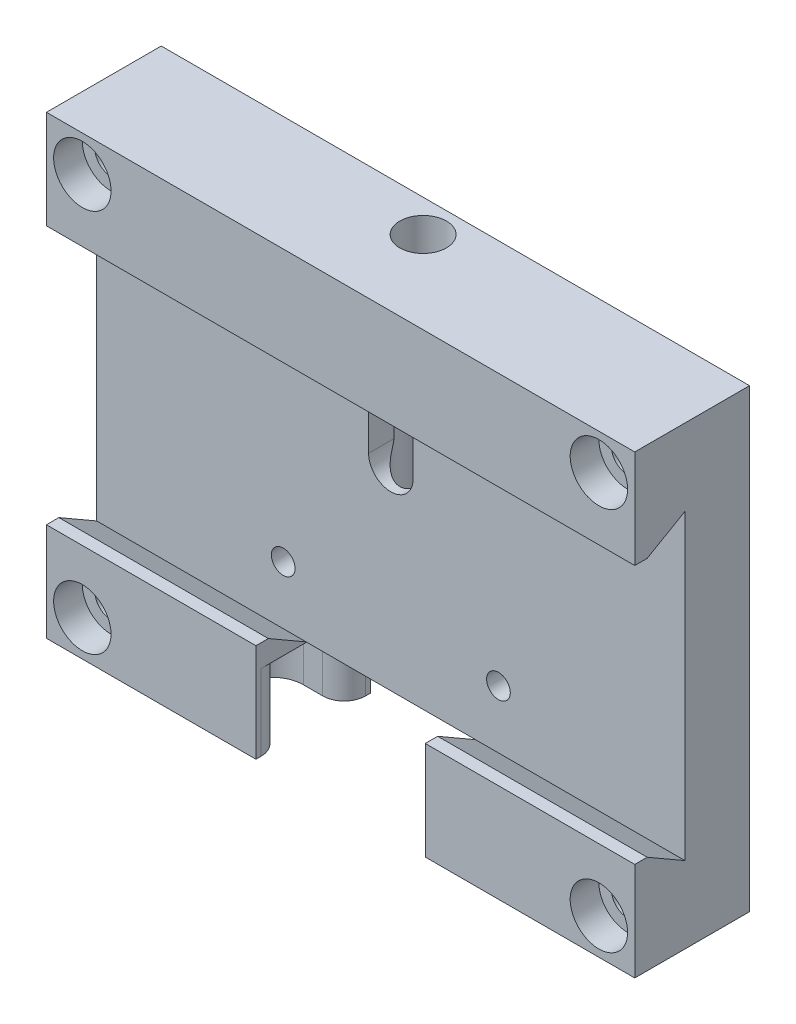
SolidWorks part; units mm, degrees
material "Сплав 2024"
ref_plane "Спереди" through (0, 0, 0) normal (0, 0, 1) x (1, 0, 0)
ref_plane "Сверху" through (0, 0, 0) normal (0, 1, 0) x (1, 0, 0)
ref_plane "Справа" through (0, 0, 0) normal (1, 0, 0) x (0, 0, -1)
sketch "Эскиз1" plane through (0, 0, 0) normal (0, 0, 1) x (1, 0, 0)
  line L1 (0, 0) -> (82, 0)
  line L2 (0, 0) -> (0, -63.5)
  line L3 (0, -63.5) -> (82, -63.5)
  line L4 (82, 0) -> (82, -63.5)
  dimension "D1" = 63.5
  dimension "D2" = 82
extrude "Бобышка-Вытянуть1" add sketch "Эскиз1" along normal blind 16
sketch "Эскиз2" plane through (0, 0, 0) normal (-1, 0, 0) x (0, 0, 1)
  line L0 (0, -31.75) -> (12.8711, -31.75) construction
  line L1 (0, 0) -> (0, -63.5) construction
  line L3 (16, 0) -> (16, -63.5) construction
  line L4 (9, -10.67) -> (16, -14.7115)
  line L5 (9, -10.67) -> (9, -52.83)
  line L6 (9, -52.83) -> (16, -48.7885)
  line L7 (16, -14.7115) -> (16, -48.7885)
  line L8 (9, -10.67) -> (16, -48.7885) construction
  line L9 (9, -52.83) -> (16, -14.7115) construction
  dimension "D1" = 42.16
  dimension "D2" = 60
  dimension "D3" = 60
  dimension "D4" = 7
extrude "Вырез-Вытянуть1" cut sketch "Эскиз2" against normal through all
ref_plane "Плоскость1" through (0, 0, 4) normal (0, 0, 1) x (1, 0, 0)
sketch "Эскиз11" plane through (0, 0, 0) normal (0, 0, -1) x (-1, 0, 0)
  line L0 (-82, -5) -> (0, -5) construction
  line L1 (-82, -63.5) -> (-82, 0) construction
  line L2 (0, 0) -> (0, -63.5) construction
  line L3 (-82, -58.5) -> (0, -58.5) construction
  line L4 (-82, 0) -> (0, 0) construction
  line L5 (0, -63.5) -> (-82, -63.5) construction
  line L8 (-82, -31.75) -> (0, -31.75) construction
  line L9 (-41, 0) -> (-41, -63.5) construction
  line L10 (-77, 0) -> (-77, -63.5) construction
  line L11 (-63.5, -11.75) -> (-18.5, -11.75) construction
  line L12 (-63.5, -11.75) -> (-63.5, -51.75) construction
  line L13 (-63.5, -51.75) -> (-18.5, -51.75) construction
  line L14 (-18.5, -11.75) -> (-18.5, -51.75) construction
  line L15 (-63.5, -11.75) -> (-18.5, -51.75) construction
  line L16 (-63.5, -51.75) -> (-18.5, -11.75) construction
  line L17 (-82, 0) -> (0, 0) construction
  line L18 (-82, -10.67) -> (-82, -52.83) construction
  line L19 (-5, 0) -> (-5, -63.5) construction
  line L20 (0, -10.67) -> (0, -52.83) construction
  line L21 (0, -63.5) -> (-82, -63.5) construction
  point P20 (-41, -31.75)
  dimension "D1" = 5
  dimension "D2" = 5
  dimension "D3" = 5
  dimension "D4" = 5
  dimension "D5" = 45
  dimension "D6" = 40
sketch "Эскиз15" plane through (0, 0, 16) normal (0, 0, 1) x (1, 0, 0)
  line L0 (41, 0) -> (41, -63.5) construction
  line L1 (82, 0) -> (0, 0) construction
  line L2 (0, -63.5) -> (82, -63.5) construction
  line L3 (82, -48.7885) -> (0, -48.7885) construction
  line L4 (29.2, -48.7885) -> (52.8, -48.7885)
  line L5 (29.2, -48.7885) -> (29.2, -63.5)
  line L6 (29.2, -63.5) -> (52.8, -63.5)
  line L7 (52.8, -48.7885) -> (52.8, -63.5)
  line L8 (29.2, -48.7885) -> (52.8, -63.5) construction
  line L9 (29.2, -63.5) -> (52.8, -48.7885) construction
  point P6 (41, -56.1443)
  dimension "D1" = 23.6
extrude "Вырез-Вытянуть4" cut sketch "Эскиз15" against normal up to surface (7 mm away) up to face at (41, -31.75, 9)
sketch "Эскиз16" plane through (0, 0, 9) normal (0, 0, 1) x (1, 0, 0)
  line L0 (41, 0) -> (41, -63.5) construction
  line L1 (29.2, -52.83) -> (52.8, -52.83)
  line L2 (29.2, -52.83) -> (29.2, -63.5)
  line L3 (29.2, -63.5) -> (52.8, -63.5)
  line L4 (52.8, -52.83) -> (52.8, -63.5)
  line L5 (29.2, -52.83) -> (52.8, -63.5) construction
  line L6 (29.2, -63.5) -> (52.8, -52.83) construction
  line L7 (29.2, -63.5) -> (52.8, -63.5) construction
  line L8 (82, -52.83) -> (52.8, -52.83) construction
  line L9 (52.8, -63.5) -> (52.8, -52.83) construction
  point P0 (41, -58.165)
extrude "Вырез-Вытянуть5" cut sketch "Эскиз16" against normal up to surface (9 mm away) up to face at (41, -31.75, 0)
sketch "Эскиз17" plane through (0, -52.83, 0) normal (0, -1, 0) x (1, 0, 0)
  line L0 (35.125, 5) -> (60.125, 5) construction
  line L3 (41, 9) -> (41, 0) construction
  line L4 (82, 9) -> (0, 9) construction
  line L5 (29.2, 0) -> (52.8, 0) construction
  circle A0 centre (33.5, 5) radius 2.5
  circle A1 centre (48.5, 5) radius 2.5
  dimension "D1" = 5
  dimension "D2" = 7.5
  dimension "D3" = 5
extrude "Вырез-Вытянуть6" cut sketch "Эскиз17" against normal blind 8
hole_wizard "Отверстие обработанное метчиком M4x0.72" positions "Эскиз19" profile "Эскиз18" tap size "M4x0.7" standard "Ansi Metric"
sketch "Эскиз19" plane through (0, -52.83, 0) normal (0, -1, 0) x (-1, 0, 0)
  line L0 (-41, -9) -> (-41, 0) construction
  line L1 (-35.125, -5) -> (-60.125, -5) construction
  point P0 (-41, -5)
sketch "Эскиз18" plane through (41, -52.83, 5) normal (1, 0, 0) x (0, 0, -1)
  line L0 (0, 0) -> (0, 10.9914)
  line L1 (0, 10.9914) -> (1.65, 10)
  line L2 (1.65, 10) -> (1.65, 0)
  line L5 (1.65, 0) -> (0, 0)
  line L10 (0, 10.9914) -> (-1.65, 10) construction
  line L11 (0, -6.35) -> (0, 107.95) construction
  dimension "Диаметр сверла" = 3.3
  dimension "Глубина сверла" = 10
  dimension "Угол заточки сверла" = 118
cosmetic thread "Отверстие резьбы9" parameters "D1"=8, "D2"=4
sketch "Эскиз25" plane through (0, 0, 9) normal (0, 0, 1) x (1, 0, 0)
  line L0 (41, 0) -> (41, -52.83) construction
  line L1 (82, 0) -> (0, 0) construction
  line L2 (52.8, -52.83) -> (29.2, -52.83) construction
  line L3 (41, -18.7115) -> (41, -25.7115) construction
  line L4 (44.1, -18.7115) -> (44.1, -25.7115)
  line L5 (37.9, -18.7115) -> (37.9, -25.7115)
  line L6 (82, -14.7115) -> (0, -14.7115) construction
  arc A0 (44.1, -18.7115) -> (37.9, -18.7115) centre (41, -18.7115) ccw
  arc A1 (37.9, -25.7115) -> (44.1, -25.7115) centre (41, -25.7115) ccw
  point P8 (41, -22.2115)
  dimension "D1" = 3.1
  dimension "D2" = 4
  dimension "D3" = 7
extrude "Вырез-Вытянуть7" cut sketch "Эскиз25" against normal blind 4
sketch "Эскиз26" plane through (0, 0, 0) normal (0, 1, 0) x (1, 0, 0)
  line L0 (0, -9) -> (82, -9) construction
  line L1 (0, -16) -> (0, 0) construction
  line L2 (82, -16) -> (82, 0) construction
  line L4 (82, 0) -> (0, 0) construction
  line L5 (41, 0) -> (41, -16) construction
  line L6 (82, -16) -> (0, -16) construction
  circle A0 centre (41, -4.5) radius 3.25
  dimension "D2" = 6.5
  dimension "D1" = 9
  dimension "D3" = 4.5
extrude "Вырез-Вытянуть8" cut sketch "Эскиз26" against normal blind 38
hole_wizard "Цековка для винта с внутренним шестигранником M41" positions "Эскиз29" profile "Эскиз28" counterbore size "M4" standard "Ansi Metric" end condition through all
sketch "Эскиз29" plane through (30.7592, 26.7934, 16) normal (0, 0, -1) x (-1, 0, 0)
  line L0 (-51.2408, -31.7934) -> (30.7592, -31.7934) construction
  line L1 (-46.2408, -26.7934) -> (-46.2408, -90.2934) construction
  line L2 (-51.2408, -85.2934) -> (30.7592, -85.2934) construction
  line L3 (25.7592, -26.7934) -> (25.7592, -90.2934) construction
  point P0 (-46.2408, -31.7934)
  point P6 (-46.2408, -85.2934)
  point P10 (25.7592, -85.2934)
  point P14 (25.7592, -31.7934)
sketch "Эскиз28" plane through (77, -5, 16) normal (1, 0, 0) x (0, -1, 0)
  line L0 (0, 0) -> (0, 16)
  line L1 (0, 16) -> (2.25, 16)
  line L3 (2.25, 16) -> (2.25, 4)
  line L4 (2.25, 4) -> (4, 4)
  line L5 (4, 4) -> (4, 0)
  line L7 (4, 0) -> (0, 0)
  line L11 (0, -6.35) -> (0, 107.95) construction
  dimension "Диаметр сквозного отверстия" = 4.5
  dimension "Глубина сквозного отверстия" = 16
  dimension "Диаметр цековки" = 8
  dimension "Глубина цековки" = 4
chamfer "Фаска2" distance 1 angle 90 3 edges at (67.4, -48.7885, 16) (14.6, -48.7885, 16) (41, -14.7115, 16)
sketch "Эскиз32" plane through (0, -63.5, 0) normal (0, -1, 0) x (1, 0, 0)
  line L0 (52.7, -0.2) -> (52.7, 3.7)
  line L1 (41, 9) -> (41, 0) construction
  line L2 (52.8, 9) -> (29.2, 9) construction
  line L3 (52.5, 0) -> (52.5, 3.9) construction
  line L4 (29.2, 8) -> (52.8, 8) construction
  line L5 (52.5, 3.9) -> (58.5, 3.9) construction
  line L6 (58.5, 12.1) -> (52.5, 12.1) construction
  line L7 (29.2, 0) -> (29.2, 16) construction
  line L8 (52.8, 0) -> (52.8, 9) construction
  line L9 (52.5, 12.1) -> (52.5, 16) construction
  line L10 (52.5, 16) -> (29.5, 16) construction
  line L11 (29.5, 16) -> (29.5, 12.1) construction
  line L12 (29.5, 12.1) -> (23.5, 12.1) construction
  line L13 (23.5, 3.9) -> (29.5, 3.9) construction
  line L14 (29.5, 3.9) -> (29.5, 0) construction
  line L15 (29.5, 0) -> (52.5, 0) construction
  line L16 (52.7, 3.7) -> (58.5, 3.7)
  line L17 (58.5, 12.3) -> (52.7, 12.3)
  line L18 (52.7, 12.3) -> (52.7, 16.2)
  line L19 (52.7, 16.2) -> (29.3, 16.2)
  line L20 (29.3, 16.2) -> (29.3, 12.3)
  line L21 (29.3, 12.3) -> (23.5, 12.3)
  line L22 (23.5, 3.7) -> (29.3, 3.7)
  line L23 (29.3, 3.7) -> (29.3, -0.2)
  line L24 (29.3, -0.2) -> (52.7, -0.2)
  arc A0 (58.5, 3.9) -> (58.5, 12.1) centre (58.5, 8) ccw construction
  arc A1 (23.5, 12.1) -> (23.5, 3.9) centre (23.5, 8) ccw construction
  arc A2 (58.5, 3.7) -> (58.5, 12.3) centre (58.5, 8) ccw
  arc A3 (23.5, 12.3) -> (23.5, 3.7) centre (23.5, 8) ccw
  point P7 (41, 16)
  point P20 (41, 0)
  dimension "D1" = 0.2
extrude "Вырез-Вытянуть12" cut sketch "Эскиз32" against normal blind 10.6
fillet "Скругление1" radius 3 4 edges at (52.8, -58.2, 12.3) (52.8, -58.2, 3.7) (29.2, -58.2, 3.7) (29.2, -58.2, 12.3)
sketch "Эскиз33" plane through (0, 0, 0) normal (0, 0, -1) x (-1, 0, 0)
  line L0 (0, -31.75) -> (-82, -31.75) construction
  line L1 (0, 0) -> (0, -63.5) construction
  line L2 (-82, -63.5) -> (-82, 0) construction
  line L3 (-41, 0) -> (-41, -52.83) construction
  line L4 (-82, 0) -> (0, 0) construction
  line L5 (-29.2, -52.83) -> (-52.8, -52.83) construction
  line L7 (-26, -44.75) -> (-56, -44.75) construction
  line L8 (-26, -44.75) -> (-26, -18.75) construction
  line L9 (-26, -18.75) -> (-56, -18.75) construction
  line L10 (-56, -44.75) -> (-56, -18.75) construction
  line L11 (-26, -44.75) -> (-56, -18.75) construction
  line L12 (-26, -18.75) -> (-56, -44.75) construction
  point P12 (-41, -31.75)
  dimension "D1" = 30
  dimension "D2" = 26
hole_wizard "Отверстие обработанное метчиком M4x0.73" positions "Эскиз35" profile "Эскиз34" tap size "M4x0.7" standard "Ansi Metric" end condition through all
sketch "Эскиз35" plane through (0, 0, 0) normal (0, 0, -1) x (-1, 0, 0)
  point P0 (-26, -44.75)
  point P3 (-26, -18.75)
  point P6 (-56, -18.75)
  point P9 (-56, -44.75)
sketch "Эскиз34" plane through (26, -44.75, 0) normal (1, 0, 0) x (0, 1, 0)
  line L0 (0, 0) -> (0, 16)
  line L1 (0, 16) -> (1.65, 16)
  line L2 (1.65, 16) -> (1.65, 0)
  line L5 (1.65, 0) -> (0, 0)
  line L11 (0, -6.35) -> (0, 107.95) construction
  dimension "Диаметр проходного сверла" = 3.3
  dimension "Глубина проходного сверла" = 16
cosmetic thread "Отверстие резьбы18" parameters "D2"=4
cosmetic thread "Отверстие резьбы19" parameters "D2"=4
cosmetic thread "Отверстие резьбы20" parameters "D2"=4
cosmetic thread "Отверстие резьбы21" parameters "D2"=4
